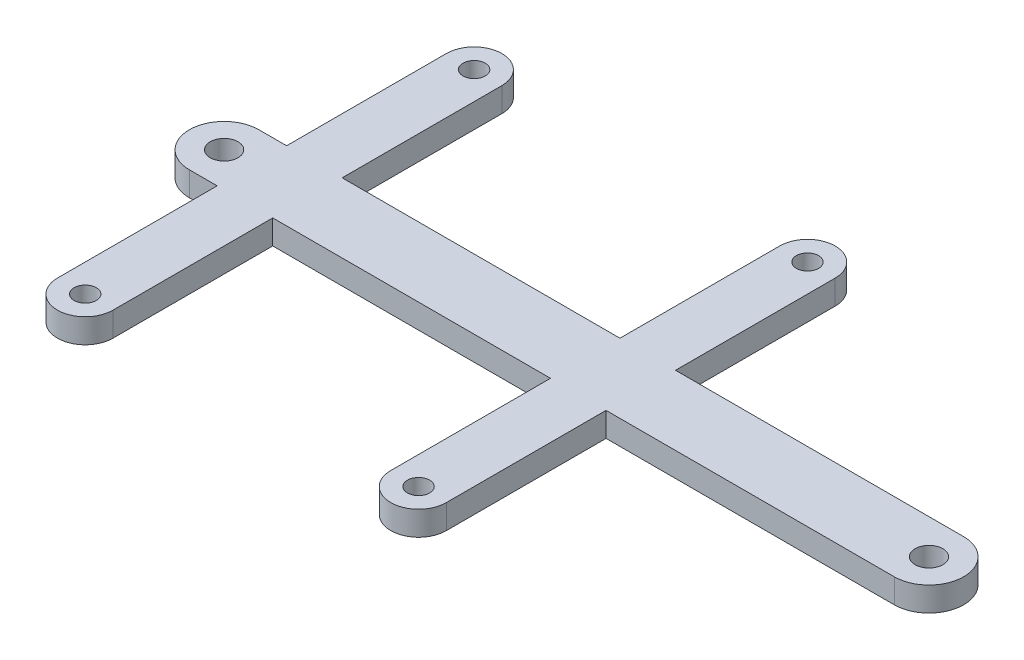
SolidWorks part; units mm, degrees
ref_plane "Front Plane" through (0, 0, 0) normal (0, 0, 1) x (1, 0, 0)
ref_plane "Top Plane" through (0, 0, 0) normal (0, 1, 0) x (1, 0, 0)
ref_plane "Right Plane" through (0, 0, 0) normal (1, 0, 0) x (0, 0, -1)
sketch "Sketch1" plane through (0, 0, 0) normal (0, 1, 0) x (1, 0, 0)
  line L0 (10, 28) -> (10, 5)
  line L4 (2, 28) -> (2, 5)
  line L5 (51.5, 5) -> (10, 5)
  line L16 (-50, 5) -> (-46, 5)
  line L17 (-38, 28) -> (-38, 5)
  line L18 (-46, 28) -> (-46, 5)
  line L19 (-38, 5) -> (2, 5)
  line L20 (0, 0) -> (15.6134, 0)
  line L21 (-38, -5) -> (2, -5)
  line L22 (-46, -28) -> (-46, -5)
  line L23 (-38, -28) -> (-38, -5)
  line L24 (51.5, -5) -> (10, -5)
  line L25 (2, -28) -> (2, -5)
  line L26 (10, -28) -> (10, -5)
  line L27 (-46, -5) -> (-50, -5)
  circle A0 centre (51.5, 0) radius 2
  arc A1 (51.5, -5) -> (51.5, 5) centre (51.5, 0) ccw
  arc A6 (-50, -5) -> (-50, 5) centre (-50, 0) cw
  circle A7 centre (-50, 0) radius 2
  circle A12 centre (6, 28) radius 1.6
  arc A13 (10, 28) -> (2, 28) centre (6, 28) ccw
  arc A14 (-38, 28) -> (-46, 28) centre (-42, 28) ccw
  circle A15 centre (-42, 28) radius 1.6
  circle A16 centre (-42, -28) radius 1.6
  arc A17 (-38, -28) -> (-46, -28) centre (-42, -28) cw
  arc A18 (10, -28) -> (2, -28) centre (6, -28) cw
  circle A19 centre (6, -28) radius 1.6
  dimension "D1" = 40
  dimension "D4" = 5
  dimension "D2" = 8
  dimension "D3" = 8
  dimension "D5" = 4
  dimension "D6" = 41.5
extrude "Boss-Extrude1" add sketch "Sketch1" along normal blind 3.5
